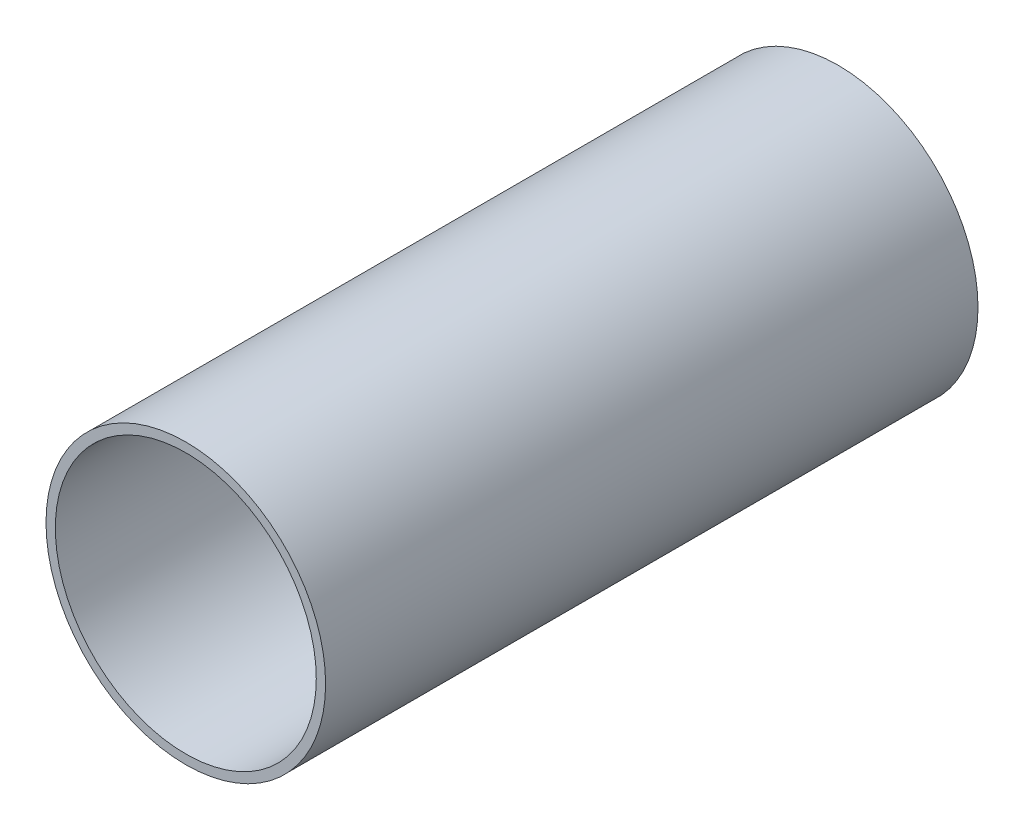
SolidWorks part; units mm, degrees
ref_plane "Front Plane" through (0, 0, 0) normal (0, 0, 1) x (1, 0, 0)
ref_plane "Top Plane" through (0, 0, 0) normal (0, 1, 0) x (1, 0, 0)
ref_plane "Right Plane" through (0, 0, 0) normal (1, 0, 0) x (0, 0, -1)
sketch "Sketch1" plane through (0, 0, 0) normal (0, 0, 1) x (1, 0, 0)
  circle A0 centre (0, 0) radius 15
  circle A1 centre (0, 0) radius 14
  dimension "D1" = 30
  dimension "D2" = 28
extrude "Boss-Extrude1" add sketch "Sketch1" along normal blind 70
